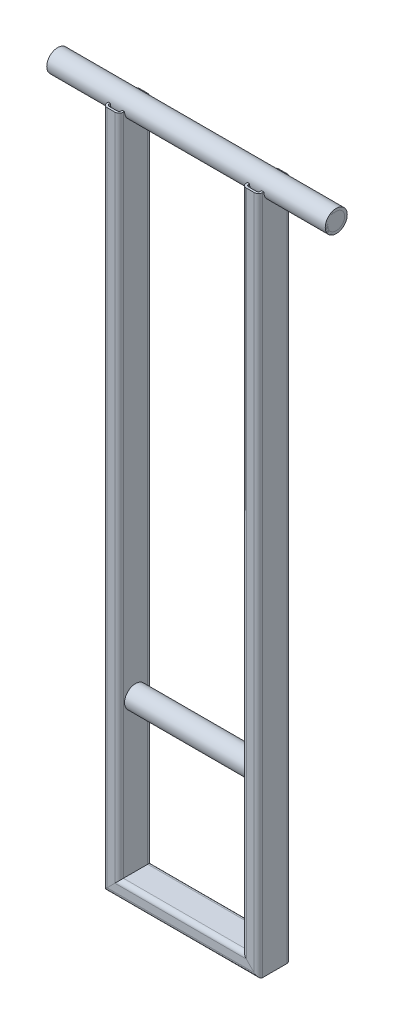
SolidWorks part; units mm, degrees
ref_plane "Front Plane" through (0, 0, 0) normal (0, 0, 1) x (1, 0, 0)
ref_plane "Top Plane" through (0, 0, 0) normal (0, 1, 0) x (1, 0, 0)
ref_plane "Right Plane" through (0, 0, 0) normal (1, 0, 0) x (0, 0, -1)
sketch "Sketch1" plane through (0, 0, 0) normal (0, 0, 1) x (1, 0, 0)
  line L0 (0, 0) -> (170, 0)
  line L1 (170, 0) -> (170, 820)
  line L2 (-85, 820) -> (255, 820)
  line L3 (0, 0) -> (0, 820)
  line L6 (0, 195) -> (170, 195)
  dimension "D1" = 170
  dimension "D2" = 340
  dimension "D3" = 85
  dimension "D4" = 820
  dimension "D5" = 625
other "Pipe 26.9 X 3.2(1)"
ref_plane "Plane1" through (-85, 820, 0) normal (1, 0, 0) x (0, 1, 0)
sketch "Sketch11" plane through (-85, 820, 0) normal (1, 0, 0) x (0, 1, 0)
  circle A0 centre (0, 0) radius 10.25
  circle A1 centre (0, 0) radius 13.45
  point P3 (0, 0)
  dimension "In_dia" = 20.5
  dimension "Out_dia" = 26.9
other "Rectangular tube 50 X 30 X 2.6(1)"
ref_plane "Plane2" through (0, 0, 0) normal (0, 1, 0) x (-1, 0, 0)
sketch "Sketch12" plane through (0, 0, 0) normal (0, 1, 0) x (-1, 0, 0)
  line L0 (-4.8, -17.4) -> (4.8, -17.4)
  line L1 (-7.4, -14.8) -> (-7.4, 14.8)
  line L2 (4.8, 17.4) -> (-4.8, 17.4)
  line L3 (7.4, 14.8) -> (7.4, -14.8)
  line L4 (-4.8, -20) -> (4.8, -20)
  line L5 (-10, -14.8) -> (-10, 14.8)
  line L6 (4.8, 20) -> (-4.8, 20)
  line L7 (10, 14.8) -> (10, -14.8)
  arc A0 (10, 14.8) -> (4.8, 20) centre (4.8, 14.8) ccw
  arc A1 (4.8, -20) -> (10, -14.8) centre (4.8, -14.8) ccw
  arc A2 (-10, -14.8) -> (-4.8, -20) centre (-4.8, -14.8) ccw
  arc A3 (-4.8, 20) -> (-10, 14.8) centre (-4.8, 14.8) ccw
  arc A4 (-4.8, 17.4) -> (-7.4, 14.8) centre (-4.8, 14.8) ccw
  arc A5 (7.4, 14.8) -> (4.8, 17.4) centre (4.8, 14.8) ccw
  arc A6 (4.8, -17.4) -> (7.4, -14.8) centre (4.8, -14.8) ccw
  arc A7 (-7.4, -14.8) -> (-4.8, -17.4) centre (-4.8, -14.8) ccw
  point P0 (0, 20)
  point P1 (10, 0)
  point P2 (0, -20)
  point P3 (-10, 0)
  point P4 (-10, 20)
  point P5 (10, 20)
  point P6 (10, -20)
  point P7 (-10, -20)
  point P8 (0, 0)
  point P33 (0, 0)
  dimension "D1" = 5.2
  dimension "Thickness" = 2.6
  dimension "V_leg" = 40
  dimension "H_leg" = 20
other "Rectangular tube 50 X 30 X 2.6(2)"
ref_plane "Plane3" through (0, 0, 0) normal (1, 0, 0) x (0, 1, 0)
sketch "Sketch13" plane through (0, 0, 0) normal (1, 0, 0) x (0, 1, 0)
  line L0 (-4.8, -17.4) -> (4.8, -17.4)
  line L1 (-7.4, -14.8) -> (-7.4, 14.8)
  line L2 (4.8, 17.4) -> (-4.8, 17.4)
  line L3 (7.4, 14.8) -> (7.4, -14.8)
  line L4 (-4.8, -20) -> (4.8, -20)
  line L5 (-10, -14.8) -> (-10, 14.8)
  line L6 (4.8, 20) -> (-4.8, 20)
  line L7 (10, 14.8) -> (10, -14.8)
  arc A0 (10, 14.8) -> (4.8, 20) centre (4.8, 14.8) ccw
  arc A1 (4.8, -20) -> (10, -14.8) centre (4.8, -14.8) ccw
  arc A2 (-10, -14.8) -> (-4.8, -20) centre (-4.8, -14.8) ccw
  arc A3 (-4.8, 20) -> (-10, 14.8) centre (-4.8, 14.8) ccw
  arc A4 (-4.8, 17.4) -> (-7.4, 14.8) centre (-4.8, 14.8) ccw
  arc A5 (7.4, 14.8) -> (4.8, 17.4) centre (4.8, 14.8) ccw
  arc A6 (4.8, -17.4) -> (7.4, -14.8) centre (4.8, -14.8) ccw
  arc A7 (-7.4, -14.8) -> (-4.8, -17.4) centre (-4.8, -14.8) ccw
  point P0 (0, 20)
  point P1 (10, 0)
  point P2 (0, -20)
  point P3 (-10, 0)
  point P4 (-10, 20)
  point P5 (10, 20)
  point P6 (10, -20)
  point P7 (-10, -20)
  point P8 (0, 0)
  point P33 (0, 0)
  dimension "D1" = 5.2
  dimension "Thickness" = 2.6
  dimension "V_leg" = 40
  dimension "H_leg" = 20
other "Trim/Extend1"
other "Trim/Extend2"
other "Trim/Extend4"
surface "Surface-Plane1"
surface "Surface-Plane2"
